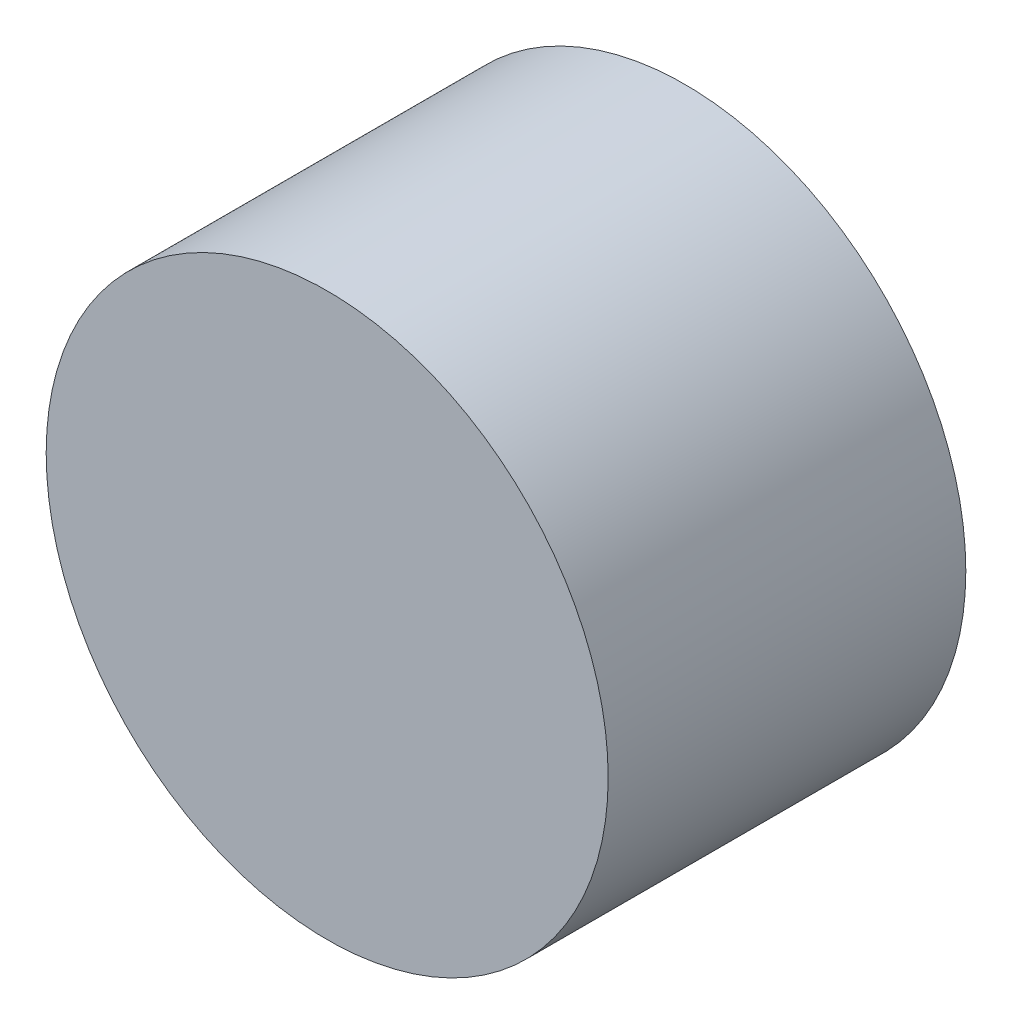
SolidWorks part; units mm, degrees
material "AISI 4340 Steel, normalized"
ref_plane "Front Plane" through (0, 0, 0) normal (0, 0, 1) x (1, 0, 0)
ref_plane "Top Plane" through (0, 0, 0) normal (0, 1, 0) x (1, 0, 0)
ref_plane "Right Plane" through (0, 0, 0) normal (1, 0, 0) x (0, 0, -1)
sketch "Sketch1" plane through (0, 0, 0) normal (0, 0, 1) x (1, 0, 0)
  circle A0 centre (0, 0) radius 1.397
  dimension "D1" = 2.794
extrude "Boss-Extrude1" add sketch "Sketch1" along normal mid plane 1.778
